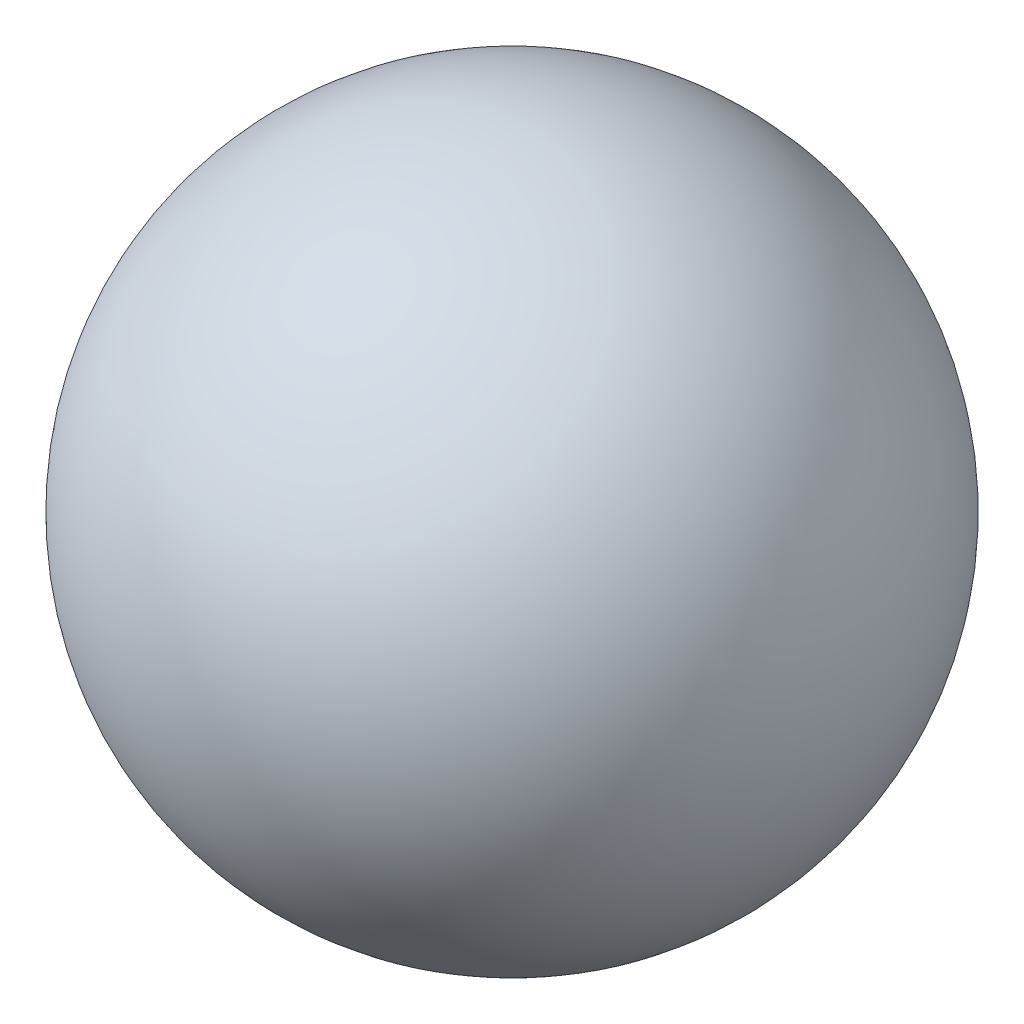
SolidWorks part; units mm, degrees
material "SBR"
ref_plane "Front Plane" through (0, 0, 0) normal (0, 0, 1) x (1, 0, 0)
ref_plane "Top Plane" through (0, 0, 0) normal (0, 1, 0) x (1, 0, 0)
ref_plane "Right Plane" through (0, 0, 0) normal (1, 0, 0) x (0, 0, -1)
sketch "Sketch1" plane through (0, 0, 0) normal (0, 0, 1) x (1, 0, 0)
  line L0 (0, 37.4466) -> (0, -44.9576) construction
  line L1 (0, -20) -> (0, 20)
  arc A0 (0, 20) -> (0, -20) centre (0, 0) ccw
  dimension "D1" = 40
revolve "Revolve2" add sketch "Sketch1" angle 360 about L0
